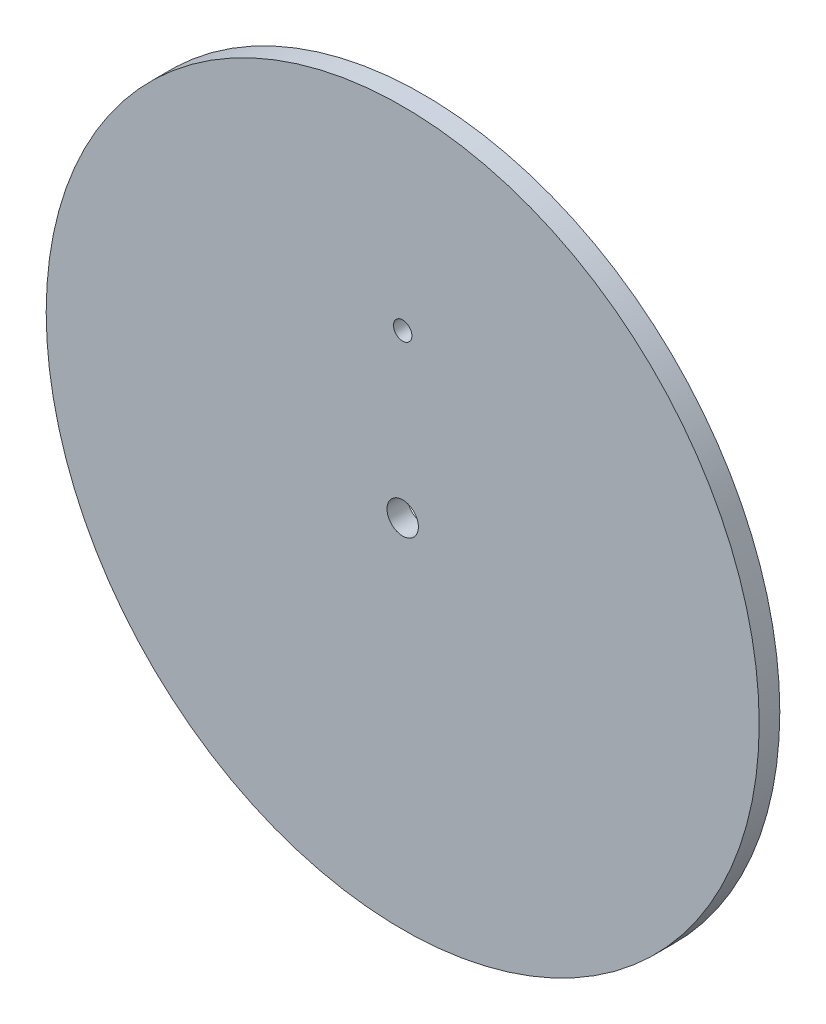
SolidWorks part; units mm, degrees
material "Maple"
ref_plane "Front Plane" through (0, 0, 0) normal (0, 0, 1) x (1, 0, 0)
ref_plane "Top Plane" through (0, 0, 0) normal (0, 1, 0) x (1, 0, 0)
ref_plane "Right Plane" through (0, 0, 0) normal (1, 0, 0) x (0, 0, -1)
sketch "Sketch2" plane through (0, 0, 0) normal (0, 0, 1) x (1, 0, 0)
  line L0 (0, 25) -> (0, 0) construction
  circle A0 centre (0, 0) radius 54.915
  circle A1 centre (0, 0) radius 2.415
  circle A2 centre (0, 25) radius 1.415
  dimension "D1" = 109.83
  dimension "D2" = 4.83
  dimension "D3" = 2.83
  dimension "D4" = 25
extrude "Boss-Extrude1" add sketch "Sketch2" along normal blind 3.175
equation "\"diameter\"=109.83"
equation "\"D1@Sketch2\"=\"diameter\""
equation "\"innerHoleDIameter\"=4.83"
equation "\"D2@Sketch2\"=\"innerHoleDIameter\""
equation "\"screwHoleDiameter\"=2.83"
equation "\"D3@Sketch2\"=\"screwHoleDiameter\""
equation "\"distance\"= 25"
equation "\"D4@Sketch2\"=\"distance\""
